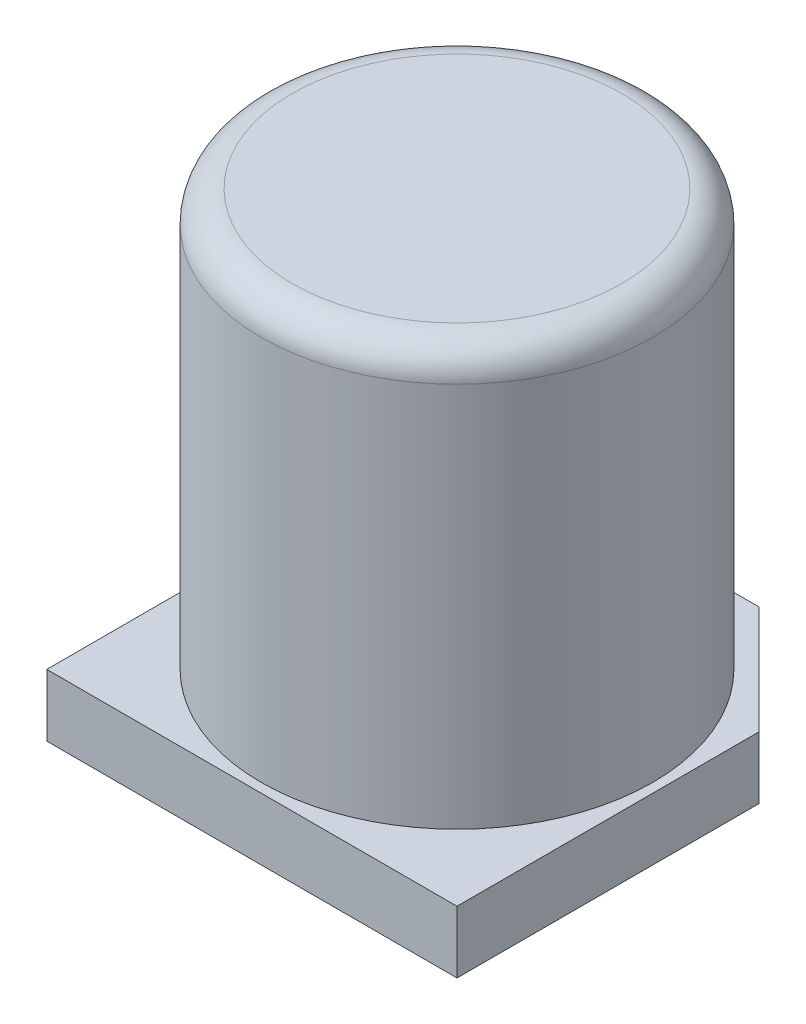
SolidWorks part; units mm, degrees
ref_plane "Front Plane" through (0, 0, 0) normal (0, 0, 1) x (1, 0, 0)
ref_plane "Top Plane" through (0, 0, 0) normal (0, 1, 0) x (1, 0, 0)
ref_plane "Right Plane" through (0, 0, 0) normal (1, 0, 0) x (0, 0, -1)
sketch "Sketch1" plane through (0, 0, 0) normal (0, 1, 0) x (1, 0, 0)
  line L0 (-3.3, 1.5625) -> (-1.5625, 3.3)
  line L1 (-3.3, 3.3) -> (3.3, 3.3)
  line L2 (-3.3, 3.3) -> (-3.3, -3.3)
  line L3 (-3.3, -3.3) -> (3.3, -3.3)
  line L4 (3.3, 3.3) -> (3.3, -3.3)
  line L5 (-3.3, 3.3) -> (3.3, -3.3) construction
  line L6 (-3.3, -3.3) -> (3.3, 3.3) construction
  line L7 (0, -3.3) -> (0, 0) construction
  line L8 (3.3, 1.5625) -> (1.5625, 3.3)
  point P0 (0, 0)
  dimension "D1" = 6.6
  dimension "D2" = 6.6
extrude "Boss-Extrude1" add sketch "Sketch1" along normal blind 1 contours L4 L8 L1 L0 L2 L3
sketch "Sketch2" plane through (0, 1, 0) normal (0, 1, 0) x (-1, 0, 0)
  circle A0 centre (0, 0) radius 3.15
  dimension "D1" = 6.3
extrude "Boss-Extrude2" add sketch "Sketch2" along normal blind 6.7
fillet "Fillet1" radius 0.5 1 edges at (0, 7.7, 3.15)
